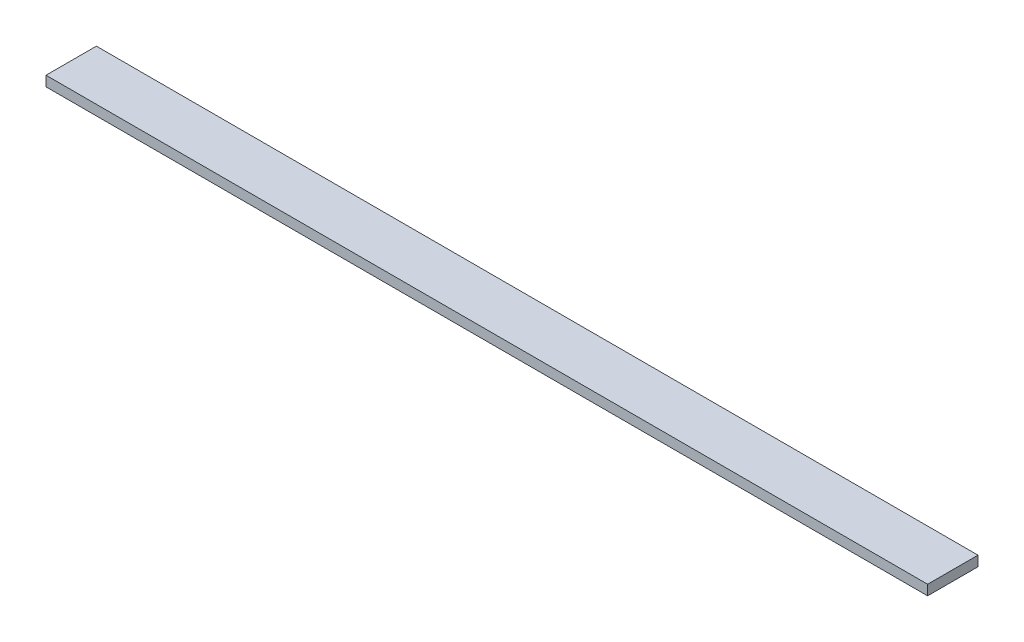
SolidWorks part; units mm, degrees
ref_plane "Спереди" through (0, 0, 0) normal (0, 0, 1) x (1, 0, 0)
ref_plane "Сверху" through (0, 0, 0) normal (0, 1, 0) x (1, 0, 0)
ref_plane "Справа" through (0, 0, 0) normal (1, 0, 0) x (0, 0, -1)
sketch "Эскиз1" plane through (0, 0, 0) normal (1, 0, 0) x (0, 0, -1)
  line L1 (0, 0) -> (20, 0)
  line L2 (0, 0) -> (0, 4)
  line L3 (0, 4) -> (20, 4)
  line L4 (20, 0) -> (20, 4)
extrude "Бобышка-Вытянуть1" add sketch "Эскиз1" along normal blind 350
